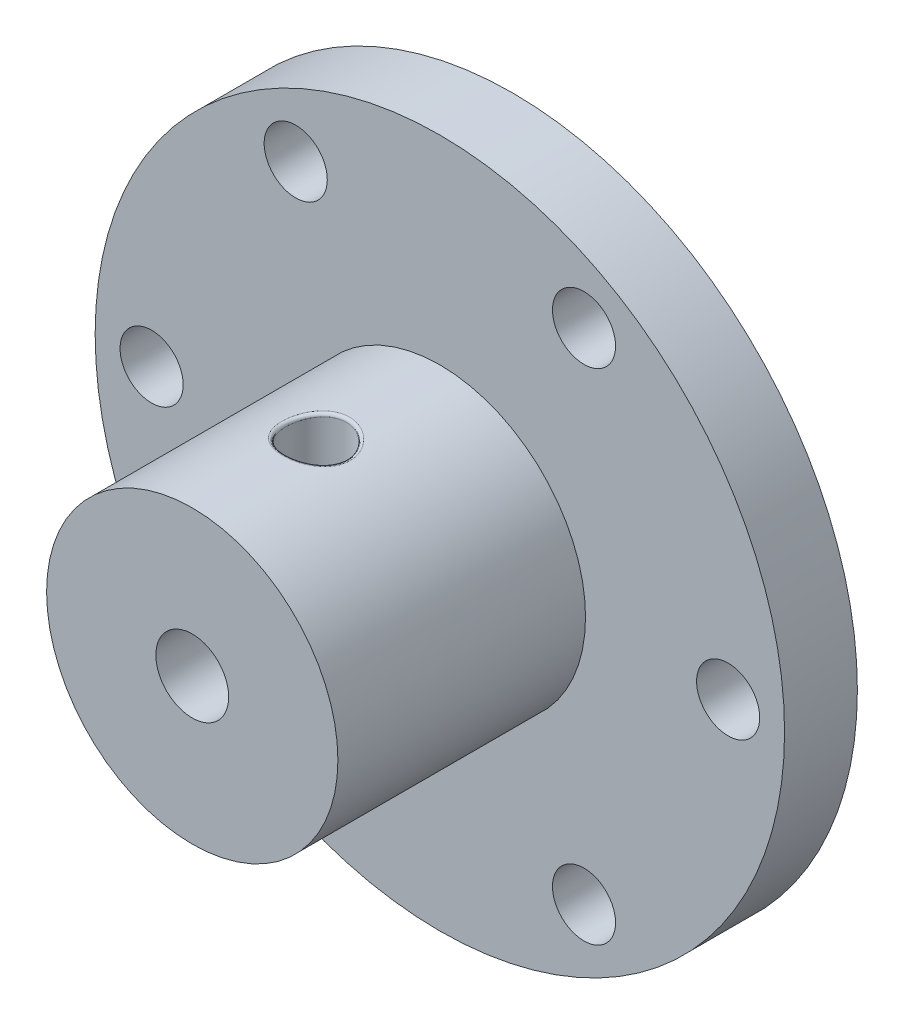
SolidWorks part; units mm, degrees
material "1060 Alloy"
ref_plane "Front Plane" through (0, 0, 0) normal (0, 0, 1) x (1, 0, 0)
ref_plane "Top Plane" through (0, 0, 0) normal (0, 1, 0) x (1, 0, 0)
ref_plane "Right Plane" through (0, 0, 0) normal (1, 0, 0) x (0, 0, -1)
sketch "Sketch1" plane through (0, 0, 0) normal (0, 0, 1) x (1, 0, 0)
  circle A0 centre (0, 0) radius 28.4
  dimension "D1" = 56.8
extrude "Boss-Extrude1" add sketch "Sketch1" along normal blind 6
sketch "Sketch2" plane through (0, 0, 6) normal (0, 0, 1) x (1, 0, 0)
  line L0 (0, 0) -> (23.75, 0) construction
  circle A0 centre (0, 0) radius 23.75 construction
  circle A1 centre (23.75, 0) radius 2.6
  circle A2 centre (11.875, -20.5681) radius 2.6
  circle A3 centre (-11.875, -20.5681) radius 2.6
  circle A4 centre (-23.75, 0) radius 2.6
  circle A5 centre (-11.875, 20.5681) radius 2.6
  circle A6 centre (11.875, 20.5681) radius 2.6
  dimension "D1" = 47.5
  dimension "D2" = 5.2
  dimension "D3" = 6
extrude "Cut-Extrude1" cut sketch "Sketch2" against normal through all
sketch "Sketch3" plane through (0, 0, 6) normal (0, 0, 1) x (1, 0, 0)
  circle A0 centre (0, 0) radius 12
  dimension "D1" = 24
extrude "Boss-Extrude2" add sketch "Sketch3" along normal blind 20.4
sketch "Sketch4" plane through (0, 0, 26.4) normal (0, 0, 1) x (1, 0, 0)
  circle A0 centre (0, 0) radius 3
  dimension "D1" = 6
extrude "Cut-Extrude2" cut sketch "Sketch4" against normal through all
sketch "Sketch5" plane through (0, 0, 0) normal (0, 1, 0) x (1, 0, 0)
  line L0 (0, -26.4) -> (0, -16.2) construction
  line L1 (-12, -26.4) -> (12, -26.4) construction
  circle A0 centre (0, -16.2) radius 2.5
  dimension "D2" = 5
  dimension "D1" = 10.2
extrude "Cut-Extrude3" cut sketch "Sketch5" along normal blind 20.4
fillet "Fillet1" radius 0.25 1 edges at (0.5148, 11.989, 18.6464)
